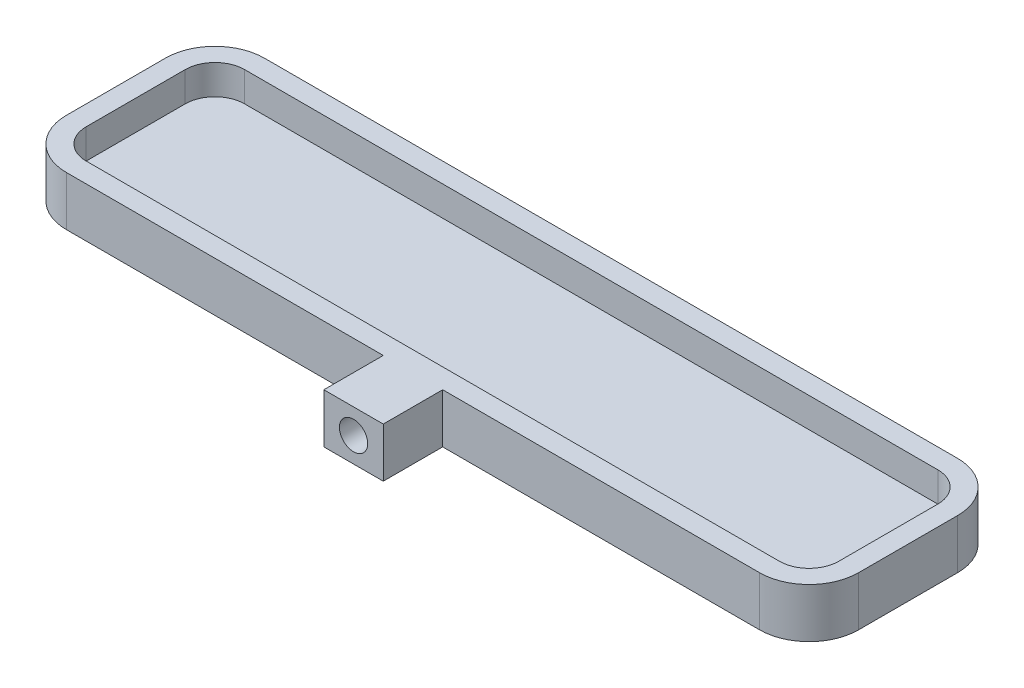
SolidWorks part; units mm, degrees
ref_plane "Front Plane" through (0, 0, 0) normal (0, 0, 1) x (1, 0, 0)
ref_plane "Top Plane" through (0, 0, 0) normal (0, 1, 0) x (1, 0, 0)
ref_plane "Right Plane" through (0, 0, 0) normal (1, 0, 0) x (0, 0, -1)
sketch "Sketch1" plane through (0, 0, 0) normal (0, 1, 0) x (1, 0, 0)
  line L1 (-40, -10) -> (40, -10)
  line L2 (-40, -10) -> (-40, 10)
  line L3 (-40, 10) -> (40, 10)
  line L4 (40, -10) -> (40, 10)
  line L5 (-40, -10) -> (40, 10) construction
  line L6 (-40, 10) -> (40, -10) construction
  point P0 (0, 0)
  dimension "D1" = 20
  dimension "D2" = 80
extrude "Boss-Extrude1" add sketch "Sketch1" along normal blind 5
fillet "Fillet1" radius 5 4 edges at (-40, 2.5, -10) (-40, 2.5, 10) (40, 2.5, -10) (40, 2.5, 10)
shell "Shell1" thickness 2
sketch "Sketch2" plane through (0, 0, 10) normal (0, 0, 1) x (1, 0, 0)
  line L0 (0, 0) -> (0, 21.2245) construction
  line L1 (-35, 0) -> (35, 0) construction
  line L2 (-35, 5) -> (35, 5) construction
  line L3 (-3, 5) -> (3, 5)
  line L4 (-3, 5) -> (-3, 0)
  line L5 (-3, 0) -> (3, 0)
  line L6 (3, 5) -> (3, 0)
  dimension "D1" = 6
extrude "Boss-Extrude2" add sketch "Sketch2" along normal blind 6
sketch "Sketch3" plane through (0, 0, 16) normal (0, 0, 1) x (1, 0, 0)
  line L0 (0, 5) -> (0, 0) construction
  line L1 (3, 5) -> (-3, 5) construction
  line L2 (-3, 2.5) -> (3, 2.5) construction
  line L3 (-3, 5) -> (-3, 0) construction
  line L4 (3, 0) -> (3, 5) construction
  line L5 (-3, 0) -> (3, 0) construction
  circle A0 centre (0, 2.5) radius 1.425
  point P13 (0, 0)
  point P14 (0, 2.5)
  point P15 (0, 2.15)
  point P16 (0, 0)
  dimension "D1" = 2.85
extrude "Cut-Extrude1" cut sketch "Sketch3" against normal blind 4
